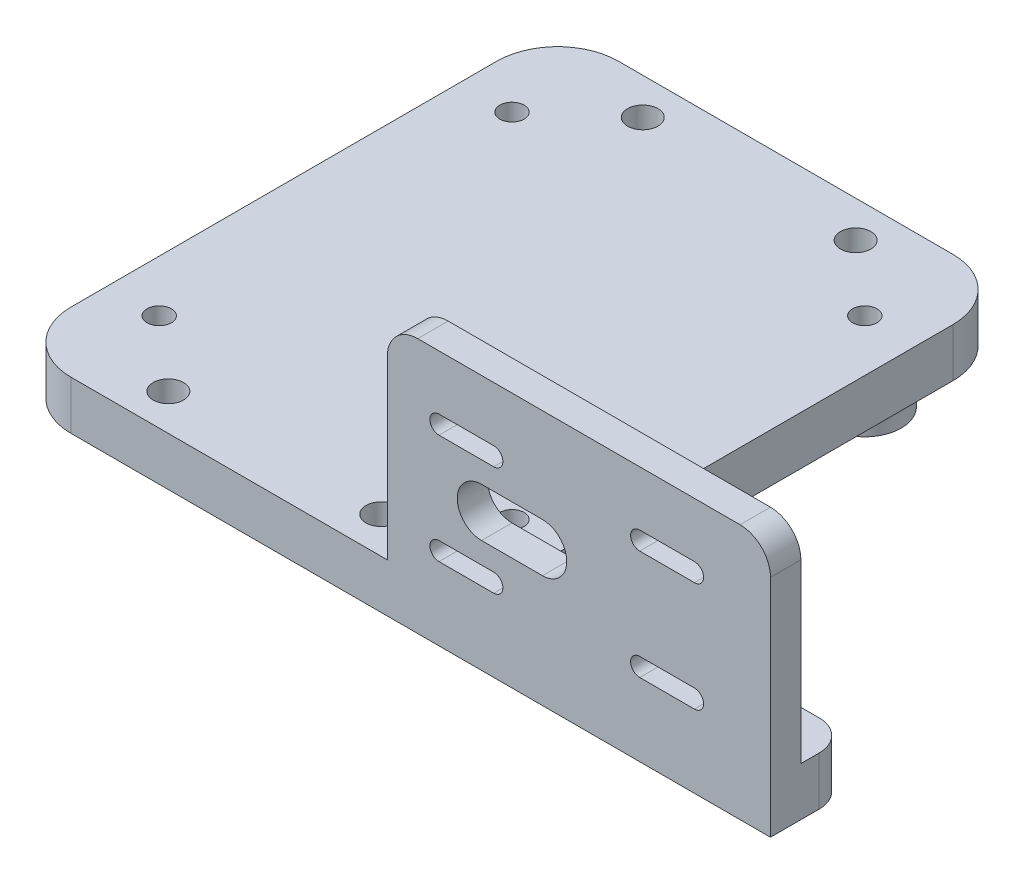
SolidWorks part; units mm, degrees
ref_plane "Front Plane" through (0, 0, 0) normal (0, 0, 1) x (1, 0, 0)
ref_plane "Top Plane" through (0, 0, 0) normal (0, 1, 0) x (1, 0, 0)
ref_plane "Right Plane" through (0, 0, 0) normal (1, 0, 0) x (0, 0, -1)
sketch "Sketch1" plane through (0, 0, 0) normal (0, 1, 0) x (1, 0, 0)
  line L1 (0, 0) -> (75, 0)
  line L2 (0, 0) -> (0, -90)
  line L3 (0, -90) -> (75, -90)
  line L4 (75, 0) -> (75, -90)
  line L5 (75, -90) -> (125, -90)
  line L6 (75, -90) -> (75, -77)
  line L7 (75, -77) -> (125, -77)
  line L8 (125, -90) -> (125, -77)
  dimension "D1" = 90
  dimension "D2" = 75
  dimension "D3" = 50
  dimension "D4" = 13
extrude "Boss-Extrude1" add sketch "Sketch1" along normal blind 8 contours L4 L1 L2 L3 | L5 L8 L7 L4
sketch "Sketch2" plane through (0, 0, 0) normal (0, -1, 0) x (1, 0, 0)
  line L0 (37.5, 0) -> (37.5, 90) construction
  line L1 (0, 0) -> (75, 0) construction
  line L2 (0, 90) -> (125, 90) construction
  circle A0 centre (37.5, 45) radius 15.5
  circle A1 centre (37.5, 45) radius 18
extrude "Boss-Extrude2" add sketch "Sketch2" along normal blind 5 contours A1 | A0
sketch "Sketch3" plane through (0, 0, 0) normal (0, -1, 0) x (1, 0, 0)
  line L0 (37.5, 45) -> (53, 45) construction
  line L2 (8.5, 16) -> (66.5, 16)
  line L3 (8.5, 16) -> (8.5, 74)
  line L4 (8.5, 74) -> (66.5, 74)
  line L5 (66.5, 16) -> (66.5, 74)
  line L6 (8.5, 16) -> (66.5, 74) construction
  line L7 (8.5, 74) -> (66.5, 16) construction
  circle A0 centre (37.5, 45) radius 15.5 construction
  circle A1 centre (8.5, 74) radius 2
  circle A2 centre (66.5, 74) radius 2
  circle A3 centre (8.5, 16) radius 2
  circle A4 centre (66.5, 16) radius 2
  dimension "D1" = 58
  dimension "D2" = 58
extrude "Cut-Extrude2" cut sketch "Sketch3" against normal through all both and the other way through all contours A1 | A2 | A3 | A4
fillet "Fillet2" radius 10 1 edges at (0, 4, 0)
fillet "Fillet3" radius 10 1 edges at (0, 4, 90)
fillet "Fillet4" radius 10 1 edges at (75, 4, 0)
sketch "Sketch5" plane through (0, 0, 0) normal (0, -1, 0) x (1, 0, 0)
  line L0 (37.5, 45) -> (37.5, 90) construction
  line L1 (10, 90) -> (125, 90) construction
  line L2 (37.5, 45) -> (75, 45)
  line L3 (37.5, 90) -> (55, 90)
  line L4 (37.5, 90) -> (37.5, 84)
  line L5 (37.5, 84) -> (55, 84)
  line L6 (55, 90) -> (55, 84)
  line L7 (75, 10) -> (75, 77) construction
  circle A0 centre (55, 84) radius 2.5
  circle A1 centre (20, 84) radius 2.5
  circle A2 centre (55, 6) radius 2.5
  circle A3 centre (20, 6) radius 2.5
  dimension "D1" = 17.5
  dimension "D2" = 6
extrude "Cut-Extrude3" cut sketch "Sketch5" against normal up to next contours A2 | A1 | A0 | A3
sketch "Sketch7" plane through (125, 0, 0) normal (1, 0, 0) x (0, 0, -1)
  line L1 (-90, 8) -> (-85, 8)
  line L2 (-90, 8) -> (-90, 42)
  line L3 (-90, 42) -> (-85, 42)
  line L4 (-85, 8) -> (-85, 42)
  dimension "D1" = 34
  dimension "D2" = 5
extrude "Boss-Extrude3" add sketch "Sketch7" against normal blind 63
fillet "Fillet5" radius 5 1 edges at (125, 42, 87.5)
fillet "Fillet6" radius 5 1 edges at (125, 4, 77)
fillet "Fillet7" radius 5 1 edges at (62, 42, 87.5)
sketch "Sketch11" plane through (0, 8, 0) normal (0, 1, 0) x (1, 0, 0)
  line L0 (20, -84) -> (55, -84) construction
  line L1 (37.5, -84) -> (37.5, -90) construction
  line L2 (10, -90) -> (62, -90) construction
sketch "Sketch12" plane through (0, 0, 90) normal (0, 0, 1) x (1, 0, 0)
  line L0 (37.5, 8) -> (77.5, 8)
  line L1 (20, 8) -> (55, 8) construction
  line L2 (62, 22.5) -> (125, 22.5) construction
  line L3 (62, 37) -> (62, 8) construction
  line L4 (125, 37) -> (125, 0) construction
  line L5 (77.5, 22.5) -> (87.5, 22.5) construction
  line L6 (77.5, 8) -> (87.5, 8)
  line L7 (77.5, 8) -> (77.5, 22.5)
  line L8 (77.5, 22.5) -> (87.5, 22.5)
  line L9 (87.5, 8) -> (87.5, 22.5)
  line L10 (77.5, 26.5) -> (87.5, 26.5)
  line L11 (77.5, 18.5) -> (87.5, 18.5)
  line L12 (70.5, 31.5) -> (79.5, 31.5) construction
  line L13 (77.5, 22.5) -> (70.5, 22.5)
  line L14 (77.5, 22.5) -> (77.5, 31.5)
  line L15 (77.5, 31.5) -> (70.5, 31.5)
  line L16 (70.5, 22.5) -> (70.5, 31.5)
  line L17 (70.5, 33) -> (79.5, 33)
  line L18 (70.5, 30) -> (79.5, 30)
  line L19 (70.5, 13.5) -> (79.5, 13.5) construction
  line L20 (70.5, 12) -> (79.5, 12)
  line L21 (70.5, 15) -> (79.5, 15)
  line L22 (103.5, 31.5) -> (112.5, 31.5) construction
  line L23 (103.5, 33) -> (112.5, 33)
  line L24 (103.5, 30) -> (112.5, 30)
  line L25 (103.5, 13.5) -> (112.5, 13.5) construction
  line L26 (103.5, 12) -> (112.5, 12)
  line L27 (103.5, 15) -> (112.5, 15)
  arc A0 (77.5, 26.5) -> (77.5, 18.5) centre (77.5, 22.5) ccw
  arc A1 (87.5, 18.5) -> (87.5, 26.5) centre (87.5, 22.5) ccw
  arc A2 (70.5, 33) -> (70.5, 30) centre (70.5, 31.5) ccw
  arc A3 (79.5, 30) -> (79.5, 33) centre (79.5, 31.5) ccw
  arc A4 (70.5, 12) -> (70.5, 15) centre (70.5, 13.5) cw
  arc A5 (79.5, 15) -> (79.5, 12) centre (79.5, 13.5) cw
  arc A6 (103.5, 33) -> (103.5, 30) centre (103.5, 31.5) ccw
  arc A7 (112.5, 30) -> (112.5, 33) centre (112.5, 31.5) ccw
  arc A8 (103.5, 12) -> (103.5, 15) centre (103.5, 13.5) cw
  arc A9 (112.5, 15) -> (112.5, 12) centre (112.5, 13.5) cw
  point P13 (82.5, 22.5)
  point P22 (75, 31.5)
  point P30 (75, 13.5)
  point P38 (108, 31.5)
  point P46 (108, 13.5)
  dimension "D2" = 7
  dimension "D4" = 2
  dimension "D1" = 10
  dimension "D3" = 9
extrude "Cut-Extrude4" cut sketch "Sketch12" against normal up to next contours L18 A3 L17 A2 | L24 A7 L23 A6 | L27 A9 L26 A8 | L21 A5 L20 A4 | L11 A1 L10 A0
sketch "Sketch13" plane through (0, 0, 0) normal (0, -1, 0) x (1, 0, 0)
  circle A0 centre (8.5, 74) radius 6
  circle A1 centre (66.5, 74) radius 6
  circle A2 centre (66.5, 16) radius 6
  circle A3 centre (8.5, 16) radius 6
  circle A4 centre (8.5, 74) radius 2
  circle A5 centre (66.5, 74) radius 2
  circle A6 centre (66.5, 16) radius 2
  circle A7 centre (8.5, 16) radius 2
  dimension "D1" = 2
  dimension "D2" = 2
  dimension "D3" = 2
  dimension "D4" = 2
extrude "Boss-Extrude4" add sketch "Sketch13" along normal blind 5
